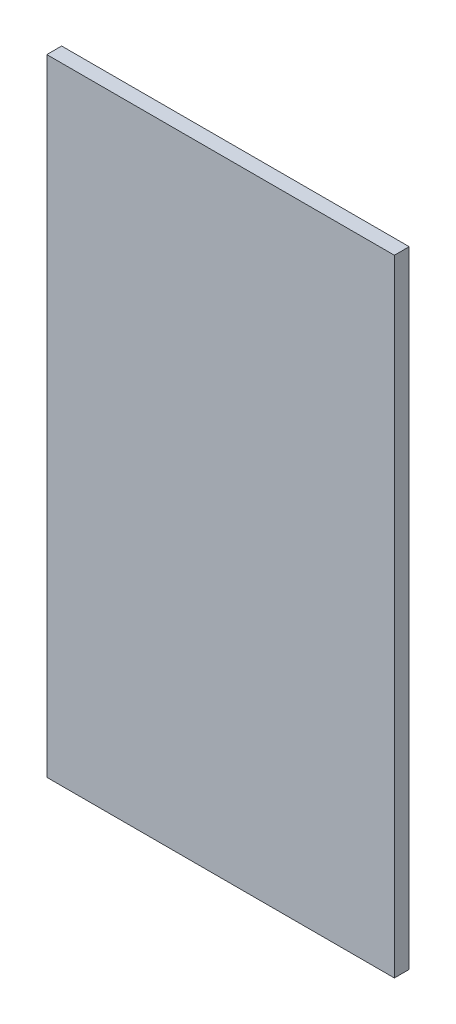
SolidWorks part; units mm, degrees
material "Perspex (TM) GS Acrylic Cast Sheet"
ref_plane "Front Plane" through (0, 0, 0) normal (0, 0, 1) x (1, 0, 0)
ref_plane "Top Plane" through (0, 0, 0) normal (0, 1, 0) x (1, 0, 0)
ref_plane "Right Plane" through (0, 0, 0) normal (1, 0, 0) x (0, 0, -1)
sketch "Sketch1" plane through (0, 0, 0) normal (0, 0, 1) x (1, 0, 0)
  line L1 (-105.5, -190) -> (105.5, -190)
  line L2 (-105.5, -190) -> (-105.5, 190)
  line L3 (-105.5, 190) -> (105.5, 190)
  line L4 (105.5, -190) -> (105.5, 190)
  line L5 (-105.5, -190) -> (105.5, 190) construction
  line L6 (-105.5, 190) -> (105.5, -190) construction
  point P0 (0, 0)
  dimension "D1" = 211
  dimension "D2" = 380
extrude "Boss-Extrude1" add sketch "Sketch1" along normal blind 9
equation "\"PCLength\"= 143mm'Length across I/O from PS to GPU"
equation "\"PCWidth\"= 340mm'Distance of longest part parallel to GPU(ussually GPU)"
equation "\"PCHeight\"= 190mm'Tallest point with mobo laying flat"
equation "\"WallThickness\"= 9mm'Thickness of each outer tank wall"
equation "\"ThermoBarrierThickness\"= 6mm'Thickness of barrier between hot side and cold side"
equation "\"HotSideGap\"= 15mm'Space in the hot side that hot fluid flows into"
equation "\"PCClearance\"= 40mm'Clearance from top of tank to top of PC"
equation "\"RadiatorHeight\"= 277.37mm'Final Height from ground of radiators"
equation "\"D1@Sketch1\"=\"PCHeight\" + \"ThermoBarrierThickness\" + \"HotSideGap\""
equation "\"D2@Sketch1\"=\"PCWidth\" + \"PCClearance\""
equation "\"D1@Boss-Extrude1\"=\"WallThickness\""
